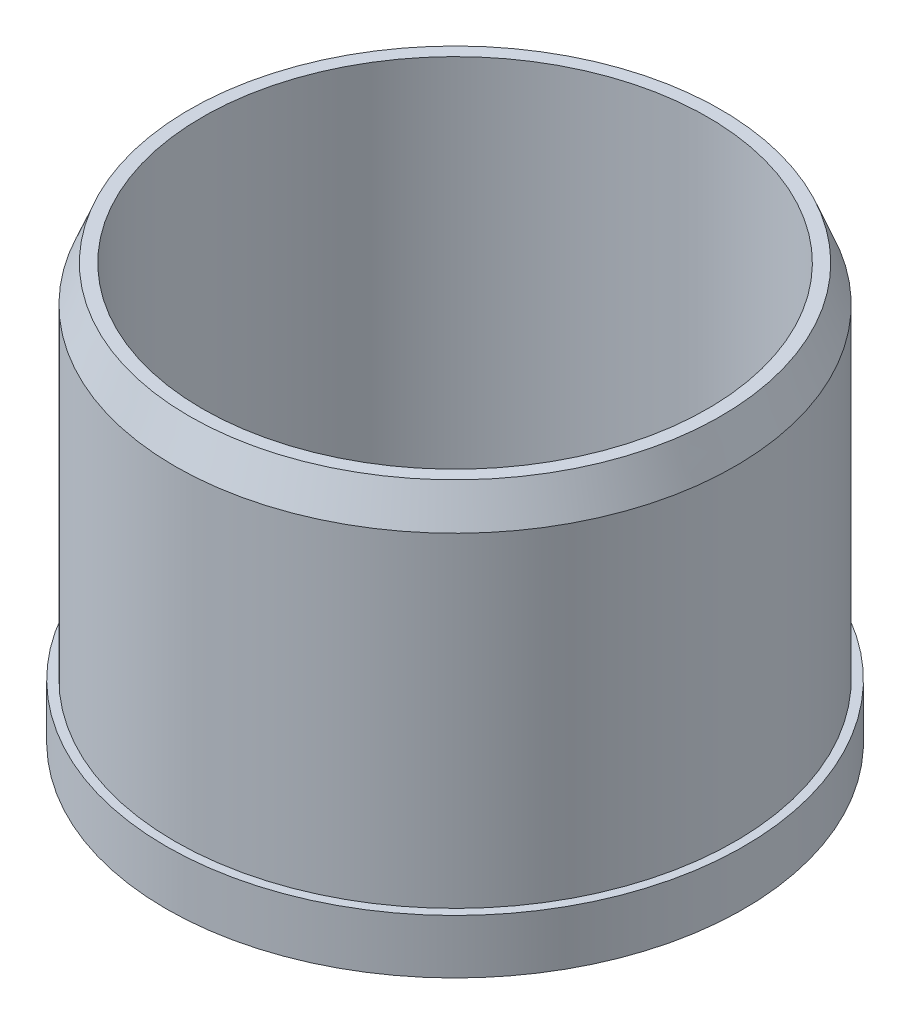
SolidWorks part; units mm, degrees
material "ABS"
ref_plane "Front Plane" through (0, 0, 0) normal (0, 0, 1) x (1, 0, 0)
ref_plane "Top Plane" through (0, 0, 0) normal (0, 1, 0) x (1, 0, 0)
ref_plane "Right Plane" through (0, 0, 0) normal (1, 0, 0) x (0, 0, -1)
sketch "Sketch1" plane through (0, 0, 0) normal (0, 1, 0) x (1, 0, 0)
  line L6 (0, 12.7) -> (0, 44.45)
  circle A0 centre (0, 0) radius 50.8
  circle A1 centre (0, 0) radius 6.5024
  circle A2 centre (0, 0) radius 12.7
  circle A3 centre (0, 0) radius 44.45
  circle A4 centre (0, 28.575) radius 12.7
  circle A5 centre (27.1764, 8.8302) radius 12.7
  circle A6 centre (16.796, -23.1177) radius 12.7
  circle A7 centre (-16.796, -23.1177) radius 12.7
  circle A8 centre (-27.1764, 8.8302) radius 12.7
  point P26 (0, 0)
  dimension "D1" = 101.6
  dimension "D2" = 13.0048
  dimension "D6" = 25.4
  dimension "D7" = 88.9
  dimension "D8" = 25.4
  dimension "D9" = 5
extrude "Boss-Extrude1" add sketch "Sketch1" along normal blind 9.525
sketch "Sketch2" plane through (0, 9.525, 0) normal (0, 1, 0) x (1, 0, 0)
  circle A0 centre (0, 0) radius 49.276
  circle A1 centre (0, 0) radius 44.45
  dimension "D1" = 98.552
  dimension "D2" = 88.9
extrude "Boss-Extrude2" add sketch "Sketch2" along normal blind 63.5
sketch "Sketch3" plane through (0, 9.525, 0) normal (0, 1, 0) x (1, 0, 0)
  circle A0 centre (0, 0) radius 12.7
  circle A2 centre (0, 0) radius 6.5024
  dimension "D1" = 25.4
  dimension "D2" = 13.0048
extrude "Boss-Extrude3" add sketch "Sketch3" along normal blind 15.875
chamfer "Chamfer1" distance 6.35 distance2 2.54 1 edges at (0, 73.025, 49.276)
sketch "Sketch4" plane through (0, 25.4, 0) normal (0, 1, 0) x (1, 0, 0)
  circle A0 centre (0, 0) radius 12.7
  circle A1 centre (0, 0) radius 6.5024
  dimension "D1" = 25.4
extrude "Boss-Extrude4" add sketch "Sketch4" along normal blind 6.35
fillet "Fillet1" radius 2.54 1 edges at (0, 31.75, 12.7)
